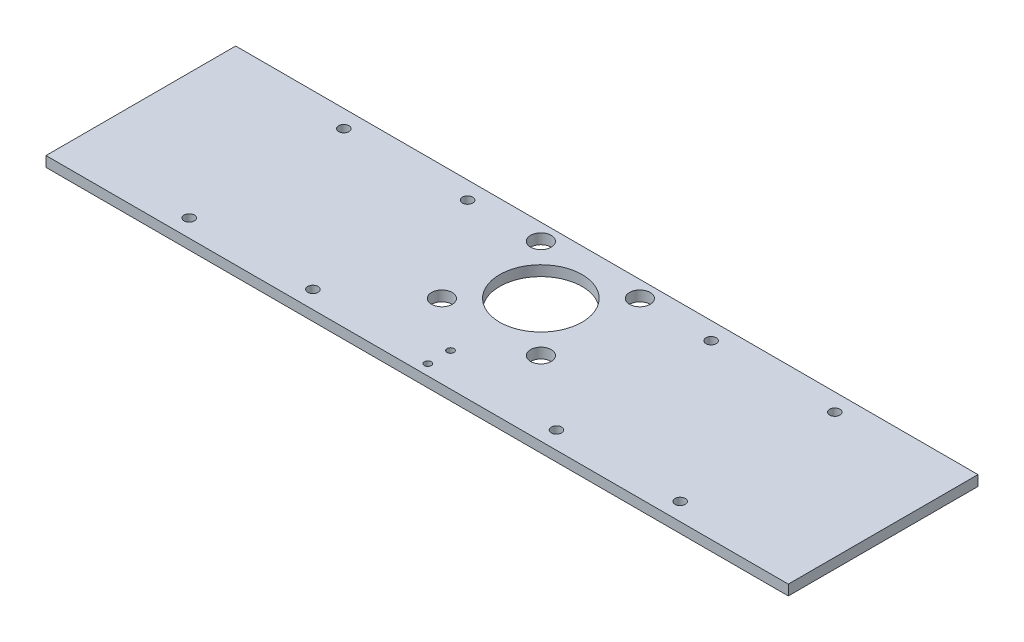
SolidWorks part; units mm, degrees
ref_plane "Front Plane" through (0, 0, 0) normal (0, 0, 1) x (1, 0, 0)
ref_plane "Top Plane" through (0, 0, 0) normal (0, 1, 0) x (1, 0, 0)
ref_plane "Right Plane" through (0, 0, 0) normal (1, 0, 0) x (0, 0, -1)
sketch "Sketch1" plane through (0, 0, 0) normal (0, 1, 0) x (1, 0, 0)
  line L1 (-228.6, 40.64) -> (228.6, 40.64)
  line L2 (-228.6, 40.64) -> (-228.6, -76.2)
  line L4 (228.6, 40.64) -> (228.6, -76.2)
  line L9 (-228.6, -76.2) -> (228.6, -76.2)
  point P0 (0, 0)
  point P10 (0, -76.2)
  dimension "D1" = 116.84
  dimension "D2" = 457.2
  dimension "D4" = 76.2
extrude "Boss-Extrude1" add sketch "Sketch1" along normal mid plane 6.35
hole_wizard "1 (1) Diameter Hole1" positions "Sketch3" profile "Sketch2" hole size "1" standard "ANSI Inch" end condition through all
sketch "Sketch3" plane through (0, 3.175, 0) normal (0, 1, 0) x (1, 0, 0)
  point P0 (0, 0)
sketch "Sketch2" plane through (0, 3.175, 0) normal (1, 0, 0) x (0, 0, 1)
  line L0 (0, 0) -> (0, 6.35)
  line L1 (0, 6.35) -> (25.4, 6.35)
  line L2 (25.4, 6.35) -> (25.4, 0)
  line L5 (25.4, 0) -> (0, 0)
  line L11 (0, -6.35) -> (0, 107.95) construction
  dimension "Thru Hole Dia." = 50.8
  dimension "Thru Hole Depth" = 6.35
hole_wizard "1/2 (0.5) Diameter Hole1" positions "Sketch5" profile "Sketch4" hole size "1/2" standard "ANSI Inch" end condition through all
sketch "Sketch5" plane through (0, 3.175, 0) normal (0, 1, 0) x (1, 0, 0)
  line L1 (-30.48, 30.48) -> (30.48, 30.48)
  line L2 (-30.48, 30.48) -> (-30.48, -30.48)
  line L3 (-30.48, -30.48) -> (30.48, -30.48)
  line L4 (30.48, 30.48) -> (30.48, -30.48)
  line L5 (-30.48, 30.48) -> (30.48, -30.48) construction
  line L6 (-30.48, -30.48) -> (30.48, 30.48) construction
  point P2 (30.48, -30.48)
  point P5 (-30.48, 30.48)
  point P6 (-30.48, -30.48)
  point P7 (30.48, 30.48)
  dimension "D1" = 60.96
sketch "Sketch4" plane through (30.48, 3.175, 30.48) normal (1, 0, 0) x (0, 0, 1)
  line L0 (0, 0) -> (0, 6.35)
  line L1 (0, 6.35) -> (6.35, 6.35)
  line L2 (6.35, 6.35) -> (6.35, 0)
  line L5 (6.35, 0) -> (0, 0)
  line L11 (0, -6.35) -> (0, 107.95) construction
  dimension "Thru Hole Dia." = 12.7
  dimension "Thru Hole Depth" = 6.35
hole_wizard "Ø4.0 (4) Diameter Hole1" positions "Sketch7" profile "Sketch6" hole size "Ø4.0" standard "ANSI Metric" end condition through all
sketch "Sketch7" plane through (0, 3.175, 0) normal (0, 1, 0) x (1, 0, 0)
  point P0 (0, -55.63)
  point P2 (0, -69.63)
  dimension "D1" = 55.63
  dimension "D2" = 14
sketch "Sketch6" plane through (0, 3.175, 55.63) normal (1, 0, 0) x (0, 0, 1)
  line L0 (0, 0) -> (0, 6.35)
  line L1 (0, 6.35) -> (2.1082, 6.35)
  line L2 (2.1082, 6.35) -> (2.1082, 0)
  line L5 (2.1082, 0) -> (0, 0)
  line L11 (0, -6.35) -> (0, 107.95) construction
  dimension "Thru Hole Dia." = 4.2164
  dimension "Thru Hole Depth" = 6.35
hole_wizard "1/4 (0.25) Diameter Hole1" positions "Sketch9" profile "Sketch8" hole size "1/4" standard "ANSI Inch" end condition through all
sketch "Sketch9" plane through (0, 3.175, 0) normal (0, 1, 0) x (1, 0, 0)
  line L1 (-75, 29.845) -> (75, 29.845)
  line L2 (-75, 29.845) -> (-75, -65.405)
  line L3 (-75, -65.405) -> (75, -65.405)
  line L4 (75, 29.845) -> (75, -65.405)
  line L5 (228.6, -17.78) -> (-228.6, -17.78) construction
  line L6 (228.6, -76.2) -> (228.6, 40.64) construction
  line L7 (-228.6, 40.64) -> (-228.6, -76.2) construction
  point P2 (75, -65.405)
  point P5 (-75, 29.845)
  point P6 (-75, -65.405)
  point P7 (75, 29.845)
  point P17 (75, -17.78)
  point P18 (0, 29.845)
  dimension "D1" = 95.25
  dimension "D2" = 150
sketch "Sketch8" plane through (75, 3.175, 65.405) normal (1, 0, 0) x (0, 0, 1)
  line L0 (0, 0) -> (0, 6.35)
  line L1 (0, 6.35) -> (3.175, 6.35)
  line L2 (3.175, 6.35) -> (3.175, 0)
  line L5 (3.175, 0) -> (0, 0)
  line L11 (0, -6.35) -> (0, 107.95) construction
  dimension "Thru Hole Dia." = 6.35
  dimension "Thru Hole Depth" = 6.35
sketch "Sketch11" plane through (0, 3.175, 0) normal (0, 1, 0) x (1, 0, 0)
  line L6 (-75, 29.845) -> (-151.2, 29.845) construction
  line L7 (-75, 29.845) -> (-75, -65.405) construction
  line L8 (-75, -65.405) -> (-151.2, -65.405) construction
  line L9 (-151.2, 29.845) -> (-151.2, -65.405) construction
  line L10 (75, -65.405) -> (151.2, -65.405) construction
  line L11 (75, -65.405) -> (75, 29.845) construction
  line L12 (75, 29.845) -> (151.2, 29.845) construction
  line L13 (151.2, -65.405) -> (151.2, 29.845) construction
  circle A0 centre (-151.2, 29.845) radius 3.175
  circle A1 centre (-151.2, -65.405) radius 3.175
  circle A2 centre (151.2, 29.845) radius 3.175
  circle A3 centre (151.2, -65.405) radius 3.175
  dimension "D2" = 6.35
  dimension "D1" = 76.2
extrude "Aux Clearance holes" cut sketch "Sketch11" against normal up to next
